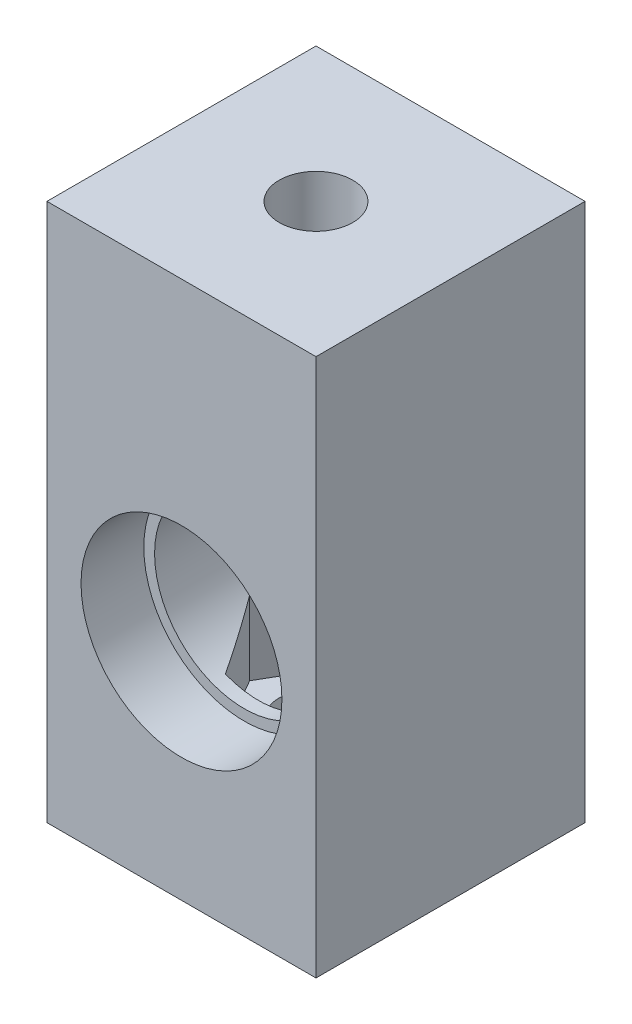
SolidWorks part; units mm, degrees
ref_plane "Спереди" through (0, 0, 0) normal (0, 0, 1) x (1, 0, 0)
ref_plane "Сверху" through (0, 0, 0) normal (0, 1, 0) x (1, 0, 0)
ref_plane "Справа" through (0, 0, 0) normal (1, 0, 0) x (0, 0, -1)
sketch "Sketch1" plane through (0, 0, 0) normal (0, 1, 0) x (1, 0, 0)
  line L1 (15, -15) -> (-15, -15)
  line L2 (15, -15) -> (15, 15)
  line L3 (15, 15) -> (-15, 15)
  line L4 (-15, -15) -> (-15, 15)
  line L5 (15, -15) -> (-15, 15) construction
  line L6 (15, 15) -> (-15, -15) construction
  point P0 (0, 0)
  dimension "D1" = 30
  dimension "D2" = 30
extrude "Boss-Extrude1" add sketch "Sketch1" along normal blind 50
sketch "Sketch2" plane through (0, 0, 15) normal (0, 0, 1) x (1, 0, 0)
  line L0 (0, 50) -> (0, 0) construction
  line L1 (-15, 50) -> (15, 50) construction
  line L2 (-15, 0) -> (15, 0) construction
  circle A0 centre (0, 25) radius 10
  dimension "D1" = 20
extrude "Cut-Extrude1" cut sketch "Sketch2" against normal through all
sketch "Sketch3" plane through (0, 0, 15) normal (0, 0, 1) x (1, 0, 0)
  circle A0 centre (0, 25) radius 11.2
  dimension "D1" = 22.4
extrude "Cut-Extrude2" cut sketch "Sketch3" against normal blind 7
sketch "Sketch4" plane through (0, 50, 0) normal (0, 1, 0) x (1, 0, 0)
  line L0 (0, 15) -> (0, -15) construction
  line L1 (15, 15) -> (-15, 15) construction
  line L2 (-15, -15) -> (15, -15) construction
  line L4 (15, -15) -> (-15, -15)
  line L5 (15, -15) -> (15, 15)
  line L6 (15, 15) -> (-15, 15)
  line L7 (-15, -15) -> (-15, 15)
  line L8 (15, -15) -> (-15, 15) construction
  line L9 (15, 15) -> (-15, -15) construction
  point P6 (0, 0)
extrude "Boss-Extrude2" add sketch "Sketch4" along normal blind 10
sketch "Sketch5" plane through (0, 60, 0) normal (0, 1, 0) x (1, 0, 0)
  line L0 (0, 15) -> (0, -15) construction
  line L1 (15, 15) -> (-15, 15) construction
  line L2 (-15, -15) -> (15, -15) construction
  circle A0 centre (0, 0) radius 4.1
  dimension "D1" = 8.2
extrude "Cut-Extrude3" cut sketch "Sketch5" against normal through all
sketch "Sketch6" plane through (0, 60, 0) normal (0, 1, 0) x (1, 0, 0)
  line L0 (15, 15) -> (-15, 15) construction
  line L1 (-3.7, 6.4086) -> (-7.4, 0)
  line L2 (-7.4, 0) -> (-3.7, -6.4086)
  line L3 (-3.7, -6.4086) -> (3.7, -6.4086)
  line L4 (3.7, -6.4086) -> (7.4, 0)
  line L5 (7.4, 0) -> (3.7, 6.4086)
  line L6 (3.7, 6.4086) -> (-3.7, 6.4086)
  circle A0 centre (0, 0) radius 7.4 construction
  dimension "D1" = 14.8
extrude "Cut-Extrude4" cut sketch "Sketch6" against normal blind 30 from offset 20
